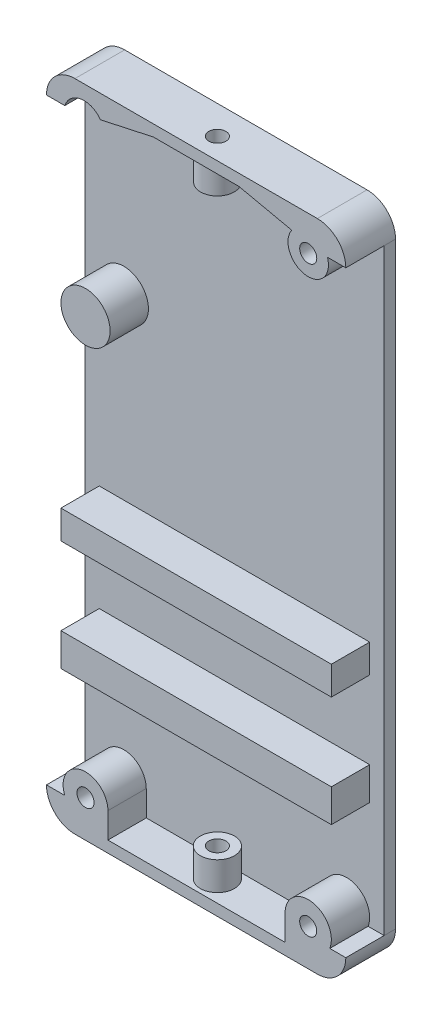
SolidWorks part; units mm, degrees
ref_plane "Front Plane" through (0, 0, 0) normal (0, 0, 1) x (1, 0, 0)
ref_plane "Top Plane" through (0, 0, 0) normal (0, 1, 0) x (1, 0, 0)
ref_plane "Right Plane" through (0, 0, 0) normal (1, 0, 0) x (0, 0, -1)
ref_plane "Plane1" through (0, 0, -28.86) normal (0, 0, 1) x (1, 0, 0)
sketch "Sketch1" plane through (0, 0, -28.86) normal (0, 0, 1) x (1, 0, 0)
  line L6 (-10.6157, 166.9489) -> (-10.6157, 62.0139)
  line L7 (-15.6157, 57.0139) -> (-58.1937, 57.0139)
  line L8 (-63.1937, 166.9489) -> (-63.1937, 62.0139)
  line L9 (-15.6157, 171.9489) -> (-58.1937, 171.9489)
  arc A0 (-63.1937, 62.0139) -> (-58.1937, 57.0139) centre (-58.1937, 62.0139) ccw
  arc A1 (-15.6157, 57.0139) -> (-10.6157, 62.0139) centre (-15.6157, 62.0139) ccw
  arc A2 (-10.6157, 166.9489) -> (-15.6157, 171.9489) centre (-15.6157, 166.9489) ccw
  arc A3 (-63.1937, 166.9489) -> (-58.1937, 171.9489) centre (-58.1937, 166.9489) cw
  dimension "D2" = 5
extrude "Boss-Extrude1" add sketch "Sketch1" against normal blind 2
sketch "Sketch2" plane through (0, 0, -28.86) normal (0, 0, 1) x (1, 0, 0)
  line L0 (-60.6537, 59.5539) -> (-60.6537, 169.4089) construction
  line L1 (-60.6537, 105.3853) -> (-13.1557, 105.3853)
  line L2 (-60.6537, 105.3853) -> (-60.6537, 100.3825)
  line L3 (-60.6537, 100.3825) -> (-13.1557, 100.3825)
  line L4 (-13.1557, 105.3853) -> (-13.1557, 100.3825)
  line L5 (-13.1557, 169.4089) -> (-13.1557, 59.5539) construction
  line L7 (-13.1557, 86.7384) -> (-60.6537, 86.7384)
  line L8 (-13.1557, 86.7384) -> (-13.1557, 80.9775)
  line L9 (-13.1557, 80.9775) -> (-60.6537, 80.9775)
  line L10 (-60.6537, 86.7384) -> (-60.6537, 80.9775)
  circle A0 centre (-17.2197, 165.8529) radius 3.556
  circle A1 centre (-17.2197, 165.8529) radius 1.5
  circle A2 centre (-56.3357, 136.6429) radius 4.318
  circle A3 centre (-17.2197, 63.4909) radius 4.064
  circle A4 centre (-17.2197, 63.4909) radius 1.5
  circle A5 centre (-56.3357, 63.4909) radius 3.937
  circle A6 centre (-56.3357, 63.4909) radius 1.5
  dimension "D1" = 3
  dimension "D2" = 3
  dimension "D3" = 3
extrude "Boss-Extrude2" add sketch "Sketch2" along normal up to surface (6.7324 mm away)
sketch "Sketch3" plane through (0, 0, -28.86) normal (0, 0, 1) x (1, 0, 0)
  line L0 (-29.4047, 169.9489) -> (-44.4047, 169.9489)
  line L4 (-12.6157, 166.9489) -> (-10.6157, 166.9489)
  line L8 (-44.4047, 171.9489) -> (-29.4047, 171.9489)
  line L10 (-15.6157, 171.9489) -> (-58.1937, 171.9489) construction
  line L11 (-12.6157, 166.9489) -> (-13.8368, 166.9489)
  line L12 (-29.4047, 169.9489) -> (-20.1086, 167.9264)
  line L13 (-44.4047, 169.9489) -> (-53.7008, 167.9264)
  line L14 (-61.1937, 166.9489) -> (-59.9726, 166.9489)
  line L16 (-61.1937, 166.9489) -> (-63.1937, 166.9489)
  line L17 (-58.1937, 171.9489) -> (-44.4047, 171.9489)
  line L19 (-29.4047, 171.9489) -> (-15.6157, 171.9489)
  line L20 (-58.1937, 57.0139) -> (-15.6157, 57.0139) construction
  line L21 (-58.1937, 57.0139) -> (-15.6157, 57.0139)
  line L22 (-52.3987, 59.0139) -> (-21.2837, 59.0139)
  line L23 (-63.1937, 62.0139) -> (-61.1937, 62.0139)
  line L24 (-10.6157, 62.0139) -> (-12.6157, 62.0139)
  line L25 (-12.6157, 62.0139) -> (-13.4336, 62.0139)
  line L26 (-21.2837, 63.4909) -> (-21.2837, 59.0139)
  line L27 (-52.3987, 63.4909) -> (-52.3987, 59.0139)
  line L28 (-61.1937, 62.0139) -> (-59.9851, 62.0139)
  line L29 (-58.1937, 59.0139) -> (-15.6157, 59.0139) construction
  arc A2 (-10.6157, 166.9489) -> (-15.6157, 171.9489) centre (-15.6157, 166.9489) ccw construction
  arc A3 (-10.6157, 166.9489) -> (-15.6157, 171.9489) centre (-15.6157, 166.9489) ccw
  circle A6 centre (-17.2197, 165.8529) radius 3.556 construction
  arc A7 (-13.8368, 166.9489) -> (-20.1086, 167.9264) centre (-17.2197, 165.8529) ccw
  arc A8 (-59.9726, 166.9489) -> (-53.7008, 167.9264) centre (-56.5897, 165.8529) cw
  arc A9 (-63.1937, 166.9489) -> (-58.1937, 171.9489) centre (-58.1937, 166.9489) cw
  arc A10 (-15.6157, 57.0139) -> (-10.6157, 62.0139) centre (-15.6157, 62.0139) ccw construction
  arc A11 (-63.1937, 62.0139) -> (-58.1937, 57.0139) centre (-58.1937, 62.0139) ccw construction
  arc A12 (-15.6157, 57.0139) -> (-10.6157, 62.0139) centre (-15.6157, 62.0139) ccw
  arc A13 (-63.1937, 62.0139) -> (-58.1937, 57.0139) centre (-58.1937, 62.0139) ccw
  circle A16 centre (-17.2197, 63.4909) radius 4.064 construction
  circle A17 centre (-56.3357, 63.4909) radius 3.937 construction
  arc A18 (-61.1937, 62.0139) -> (-58.1937, 59.0139) centre (-58.1937, 62.0139) ccw construction
  arc A19 (-59.9851, 62.0139) -> (-52.3987, 63.4909) centre (-56.3357, 63.4909) ccw
  arc A20 (-21.2837, 63.4909) -> (-13.4336, 62.0139) centre (-17.2197, 63.4909) ccw
  arc A21 (-15.6157, 59.0139) -> (-12.6157, 62.0139) centre (-15.6157, 62.0139) ccw construction
  dimension "D1" = 2
extrude "Boss-Extrude3" add sketch "Sketch3" along normal up to surface (6.7324 mm away) contours A19 L27 L22 L26 A20 L25 L24 A12 L21 A13 L23 L28 | A8 L13 L0 L12 A7 L11 L4 A3 L19 L8 L17 A9 L16 L14
sketch "Sketch4" plane through (0, 57.0139, 0) normal (0, -1, 0) x (1, 0, 0)
  line L0 (-58.1937, -30.86) -> (-15.6157, -30.86) construction
  line L2 (-15.6157, -30.86) -> (-15.6157, -22.1276) construction
  circle A0 centre (-36.9047, -25.86) radius 1.5
  dimension "D1" = 3
  dimension "D2" = 5
  dimension "D3" = 21.289
extrude "Cut-Extrude1" cut sketch "Sketch4" against normal blind 10
sketch "Sketch5" plane through (0, 171.9489, 0) normal (0, 1, 0) x (1, 0, 0)
  line L0 (-15.6157, 30.86) -> (-58.1937, 30.86) construction
  line L1 (-15.6157, 30.86) -> (-15.6157, 22.1276) construction
  circle A0 centre (-36.9047, 25.86) radius 1.5
  dimension "D1" = 3
  dimension "D2" = 5
  dimension "D3" = 21.289
extrude "Cut-Extrude2" cut sketch "Sketch5" against normal blind 10
sketch "Sketch6" plane through (0, 169.9489, 0) normal (0, -1, 0) x (1, 0, 0)
  circle A0 centre (-36.9047, -25.86) radius 2.95
  circle A1 centre (-36.9047, -25.86) radius 1.5
  dimension "D1" = 5.9
extrude "Boss-Extrude5" add sketch "Sketch6" along normal blind 5
sketch "Sketch7" plane through (0, 59.0139, 0) normal (0, 1, 0) x (1, 0, 0)
  circle A0 centre (-36.9047, 25.86) radius 2.995
  circle A1 centre (-36.9047, 25.86) radius 1.5
  dimension "D1" = 5.99
extrude "Boss-Extrude6" add sketch "Sketch7" along normal blind 5
